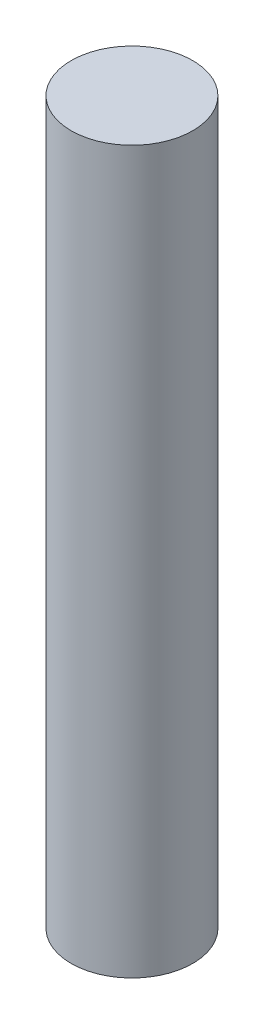
SolidWorks part; units mm, degrees
ref_plane "Front Plane" through (0, 0, 0) normal (0, 0, 1) x (1, 0, 0)
ref_plane "Top Plane" through (0, 0, 0) normal (0, 1, 0) x (1, 0, 0)
ref_plane "Right Plane" through (0, 0, 0) normal (1, 0, 0) x (0, 0, -1)
sketch "Sketch1" plane through (0, 0, 0) normal (0, 1, 0) x (1, 0, 0)
  circle A0 centre (0, 0) radius 77
  circle A1 centre (0, 0) radius 72
  dimension "D1" = 154
  dimension "D2" = 5
extrude "Extrude1" add sketch "Sketch1" along normal mid plane 908.4
sketch "Sketch2" plane through (0, 454.2, 0) normal (0, 1, 0) x (1, 0, 0)
  circle A0 centre (0, 0) radius 77
extrude "Extrude2" add sketch "Sketch2" along normal blind 5
